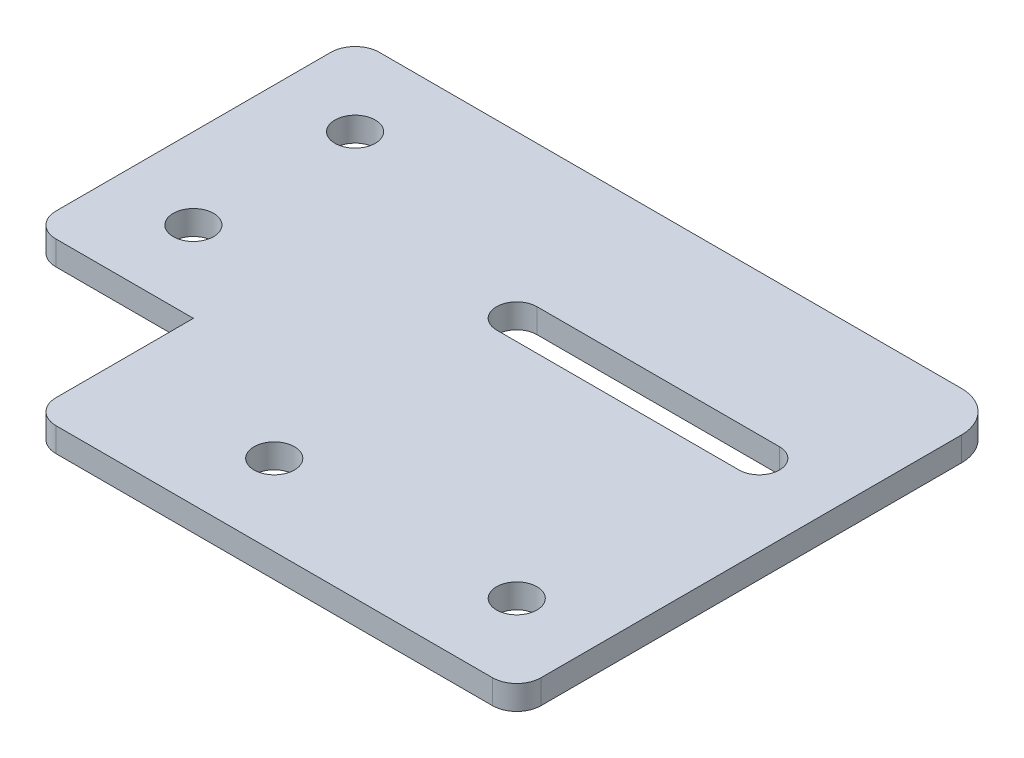
SolidWorks part; units mm, degrees
ref_plane "Front Plane" through (0, 0, 0) normal (0, 0, 1) x (1, 0, 0)
ref_plane "Top Plane" through (0, 0, 0) normal (0, 1, 0) x (1, 0, 0)
ref_plane "Right Plane" through (0, 0, 0) normal (1, 0, 0) x (0, 0, -1)
sketch "Sketch1" plane through (0, 0, 0) normal (0, 1, 0) x (1, 0, 0)
  line L0 (0, 19.5839) -> (0, 53.5839)
  line L1 (3, 56.5839) -> (75, 56.5839)
  line L2 (80, 51.5839) -> (80, -0.4161)
  line L3 (23, -3.4161) -> (77, -3.4161)
  line L4 (3, 16.5839) -> (20, 16.5839)
  line L5 (20, 16.5839) -> (20, -0.4161)
  line L6 (0, 36.5839) -> (80, 36.5839) construction
  line L7 (40, 36.5839) -> (70, 36.5839) construction
  line L8 (40, 39.0839) -> (70, 39.0839)
  line L9 (40, 34.0839) -> (70, 34.0839)
  circle A0 centre (10, 26.5839) radius 2.5
  circle A1 centre (40, 6.5839) radius 2.5
  circle A2 centre (70, 6.5839) radius 2.5
  arc A3 (23, -3.4161) -> (20, -0.4161) centre (23, -0.4161) cw
  arc A4 (3, 16.5839) -> (0, 19.5839) centre (3, 19.5839) cw
  arc A5 (77, -3.4161) -> (80, -0.4161) centre (77, -0.4161) ccw
  arc A6 (0, 53.5839) -> (3, 56.5839) centre (3, 53.5839) cw
  arc A7 (80, 51.5839) -> (75, 56.5839) centre (75, 51.5839) ccw
  circle A8 centre (10, 46.5839) radius 2.5
  arc A9 (40, 39.0839) -> (40, 34.0839) centre (40, 36.5839) ccw
  arc A10 (70, 34.0839) -> (70, 39.0839) centre (70, 36.5839) ccw
  point P15 (20, -3.4161)
  point P18 (0, 16.5839)
  point P21 (80, -3.4161)
  point P24 (0, 56.5839)
  point P33 (55, 36.5839)
  dimension "D2" = 10
  dimension "D4" = 10
  dimension "D6" = 10
  dimension "D7" = 20
  dimension "D9" = 10
  dimension "D10" = 3
  dimension "D11" = 5
  dimension "D12" = 10
  dimension "D13" = 5
  dimension "D14" = 30
  dimension "D15" = 2.5
  dimension "D1" = 20
  dimension "D3" = 20
  dimension "D5" = 40
  dimension "D8" = 60
extrude "Boss-Extrude2" add sketch "Sketch1" along normal blind 3
sketch "Sketch2" plane through (0, 3, 0) normal (0, 1, 0) x (1, 0, 0)
  line L0 (40, 36.5839) -> (70, 36.5839)
sketch "Sketch3" plane through (0, 0, 0) normal (0, -1, 0) x (1, 0, 0)
  line L0 (40, -36.5839) -> (70, -36.5839)
